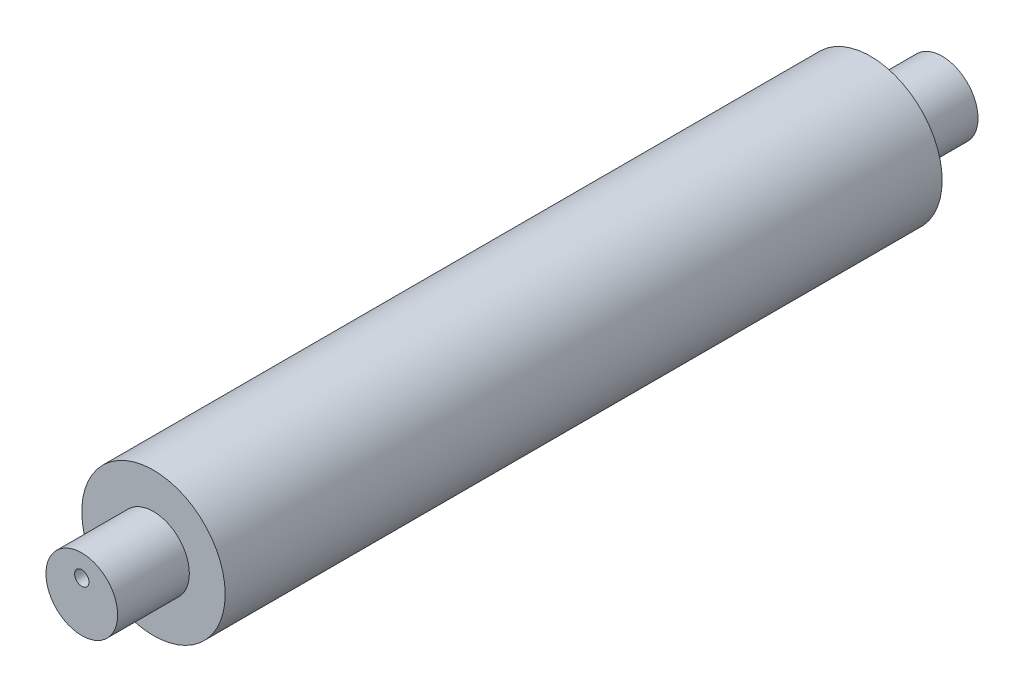
SolidWorks part; units mm, degrees
ref_plane "Front Plane" through (0, 0, 0) normal (0, 0, 1) x (1, 0, 0)
ref_plane "Top Plane" through (0, 0, 0) normal (0, 1, 0) x (1, 0, 0)
ref_plane "Right Plane" through (0, 0, 0) normal (1, 0, 0) x (0, 0, -1)
sketch "Sketch9" plane through (0, 0, 0) normal (0, 0, 1) x (1, 0, 0)
  circle A0 centre (0, 0) radius 25
  dimension "D1" = 50
extrude "Boss-Extrude1" add sketch "Sketch9" along normal mid plane 250
sketch "Sketch10" plane through (0, 0, 0) normal (0, 0, 1) x (1, 0, 0)
  circle A0 centre (0, 0) radius 12.5
  dimension "D1" = 25
extrude "Boss-Extrude4" add sketch "Sketch10" along normal mid plane 300
sketch "Sketch19" plane through (0, 0, 150) normal (0, 0, 1) x (1, 0, 0)
  circle A0 centre (0, 4.9108) radius 2.5
sketch "Sketch20" plane through (0, 0, -150) normal (0, 0, -1) x (-1, 0, 0)
  circle A0 centre (0, 4.9108) radius 2.5
extrude "Cut-Extrude5" cut sketch "Sketch20" against normal blind 20
extrude "Cut-Extrude6" cut sketch "Sketch19" against normal blind 20 contours A0
sketch "Sketch21" plane through (0, 0, 0) normal (0, 0, 1) x (1, 0, 0)
